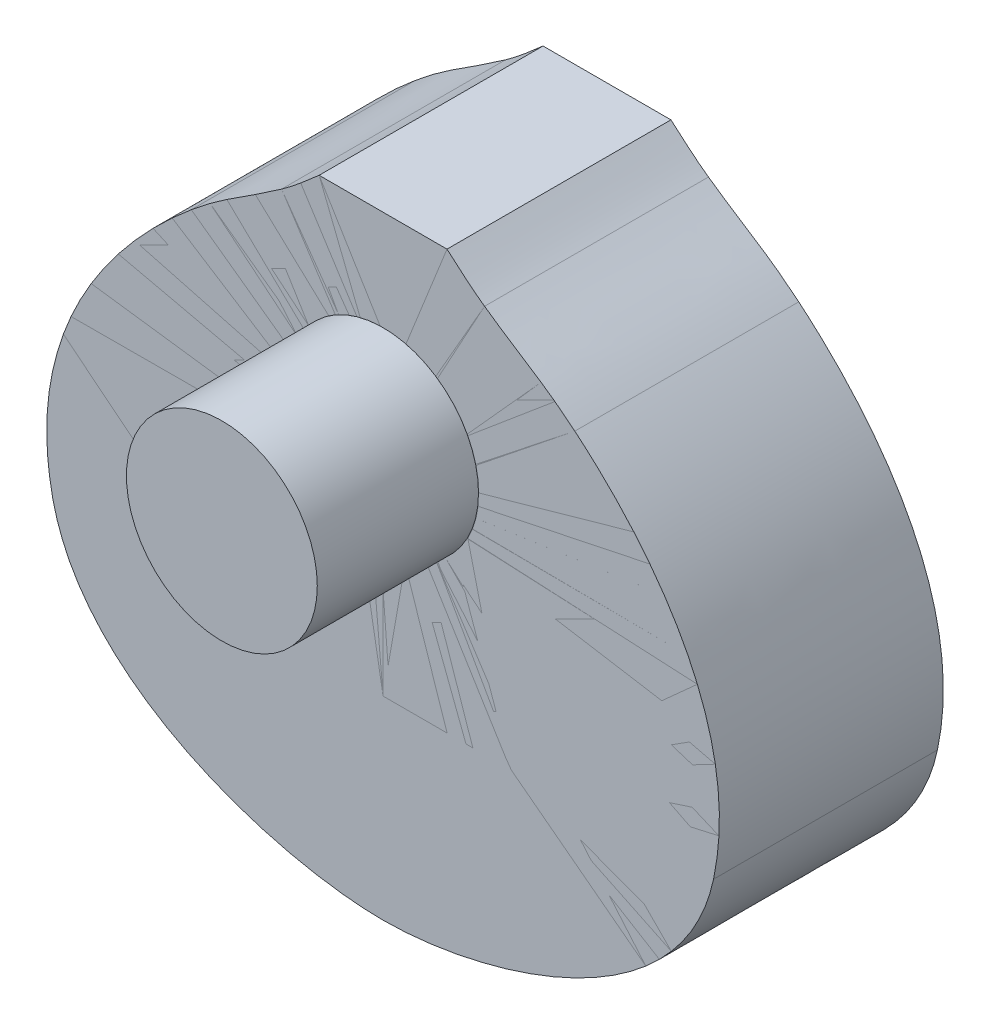
SolidWorks part; units mm, degrees
ref_plane "Alzado" through (0, 0, 0) normal (0, 0, 1) x (1, 0, 0)
ref_plane "Planta" through (0, 0, 0) normal (0, 1, 0) x (1, 0, 0)
ref_plane "Vista lateral" through (0, 0, 0) normal (1, 0, 0) x (0, 0, -1)
sketch "Croquis1" plane through (0, 0, 0) normal (0, 0, 1) x (1, 0, 0)
  line L0 (-28.5608, 136.9164) -> (0, 136.9164)
  line L3 (0, 136.9164) -> (0, -136.9164)
  spline S0 degree 3 poles (-147.5785, -47.2765) (-163.1102, 25.4873) (-105.3607, 78.5809) (-85.6394, 95.0588) knots 0 0 0 0 1 1 1 1
  spline S1 degree 3 poles (-85.6394, 95.0588) (-70.7787, 107.4754) (-62.7858, 110.8395) (-45.3232, 123.1886) knots 0 0 0 0 1 1 1 1
  spline S2 degree 3 poles (-45.3232, 123.1886) (-39.5023, 127.305) (-33.9335, 132.1947) (-28.5608, 136.9164) knots 0 0 0 0 1 1 1 1
  spline S7 degree 3 poles (0, -136.9164) (-46.4413, -136.9164) (-133.8334, -111.6704) (-147.5785, -47.2765) knots 0 0 0 0 1 1 1 1
  dimension "D1" = 273.8328
sketch "Croquis3" plane through (0, 0, 0) normal (0, 0, 1) x (1, 0, 0)
  line L0 (0, 136.9164) -> (0, -136.9164)
  line L1 (0, 136.9164) -> (28.5608, 136.9164)
  spline S0 degree 3 poles (0, -136.9164) (46.4413, -136.9164) (133.8334, -111.6704) (147.5785, -47.2765) knots 0 0 0 0 1 1 1 1
  spline S1 degree 3 poles (147.5785, -47.2765) (163.1102, 25.4873) (105.3607, 78.5809) (85.6394, 95.0588) knots 0 0 0 0 1 1 1 1
  spline S2 degree 3 poles (85.6394, 95.0588) (70.7787, 107.4754) (62.7858, 110.8395) (45.3232, 123.1886) knots 0 0 0 0 1 1 1 1
  spline S3 degree 3 poles (45.3232, 123.1886) (39.5023, 127.305) (33.9335, 132.1947) (28.5608, 136.9164) knots 0 0 0 0 1 1 1 1
extrude "Saliente-Extruir1" add sketch "Croquis1" along normal blind 100
extrude "Saliente-Extruir2" add sketch "Croquis3" along normal blind 100
sketch "Croquis8" plane through (0, 0, 100) normal (0, 0, 1) x (1, 0, 0)
  line L0 (57.282, -50.2301) -> (0, -50.2301)
  line L2 (0, 136.9164) -> (0, 92.3065)
  line L3 (28.5608, 136.9164) -> (0, 136.9164)
  line L4 (57.282, -50.2301) -> (57.282, -80.2301)
  line L5 (0, -80.2301) -> (57.282, -80.2301)
  line L6 (0, 6.7699) -> (0, -50.2301)
  line L7 (0, -80.2301) -> (0.1981, -136.0953)
  line L8 (0, -136.9164) -> (0.1981, -136.0953)
  arc A0 (0, 92.3065) -> (0, 6.7699) centre (0, 49.5382) cw
  spline S0 degree 3 poles (0, -136.9164) (46.4413, -136.9164) (133.8334, -111.6704) (147.5785, -47.2765) knots 0 0 0 0 1 1 1 1
  spline S1 degree 3 poles (45.3232, 123.1886) (39.5023, 127.305) (33.9335, 132.1947) (28.5608, 136.9164) knots 0 0 0 0 1 1 1 1
  spline S2 degree 3 poles (85.6394, 95.0588) (70.7787, 107.4754) (62.7858, 110.8395) (45.3232, 123.1886) knots 0 0 0 0 1 1 1 1
  spline S3 degree 3 poles (147.5785, -47.2765) (163.1102, 25.4873) (105.3607, 78.5809) (85.6394, 95.0588) knots 0 0 0 0 1 1 1 1
sketch "Croquis10" plane through (0, 0, 100) normal (0, 0, 1) x (1, 0, 0)
  line L0 (-28.5608, 136.9164) -> (0, 136.9164)
  line L1 (0, 136.9164) -> (0, 92.3065)
  line L2 (0, -50.2301) -> (-57.2, -50.2301)
  line L3 (0, 6.7699) -> (0, 92.3065) construction
  line L5 (0, -80.2301) -> (-57.2, -80.2301)
  line L6 (-57.2, -80.2301) -> (-57.2, -50.2301)
  line L7 (0, 6.7699) -> (0, -50.2301)
  line L8 (0, -80.2301) -> (0, -136.9164)
  arc A0 (0, 92.3065) -> (0, 6.7699) centre (0, 49.5382) ccw
  spline S0 degree 3 poles (-147.5785, -47.2765) (-163.1102, 25.4873) (-105.3607, 78.5809) (-85.6394, 95.0588) knots 0 0 0 0 1 1 1 1
  spline S1 degree 3 poles (-85.6394, 95.0588) (-70.7787, 107.4754) (-62.7858, 110.8395) (-45.3232, 123.1886) knots 0 0 0 0 1 1 1 1
  spline S2 degree 3 poles (-45.3232, 123.1886) (-39.5023, 127.305) (-33.9335, 132.1947) (-28.5608, 136.9164) knots 0 0 0 0 1 1 1 1
  spline S3 degree 3 poles (0, -136.9164) (-46.4413, -136.9164) (-133.8334, -111.6704) (-147.5785, -47.2765) knots 0 0 0 0 1 1 1 1
  point P5 (0, 49.5382)
surface "Superficie-Plano9" sketch "Croquis8"
sketch "Croquis14" plane through (0, 0, 100) normal (0, 0, 1) x (1, 0, 0)
  line L0 (0, -50.2301) -> (0, -80.2301)
  line L1 (0, -80.2301) -> (57.282, -80.2301)
  line L2 (57.282, -80.2301) -> (57.282, -50.2301)
  line L3 (57.282, -50.2301) -> (0, -50.2301)
surface "Superficie-Plano10" sketch "Croquis14"
surface "Superficie-Plano2" sketch "Croquis10"
sketch "Croquis13" plane through (0, 0, 100) normal (0, 0, 1) x (1, 0, 0)
  line L0 (0, 136.9164) -> (0, -136.9164) construction
  circle A0 centre (0, 49.6595) radius 42.6235
  point P0 (0, 92.283)
  point P1 (0, 7.036)
extrude "Saliente-Extruir3" add sketch "Croquis13" along normal blind 72
sketch "Croquis15" plane through (0, 0, 100) normal (0, 0, 1) x (1, 0, 0)
  line L0 (0, -50.2301) -> (-57.2, -50.2301)
  line L1 (-57.2, -50.2301) -> (-57.2, -80.2301)
  line L2 (-57.2, -80.2301) -> (0, -80.2301)
  line L3 (0, -80.2301) -> (0, -50.2301)
surface "Superficie-Plano11" sketch "Croquis15"
